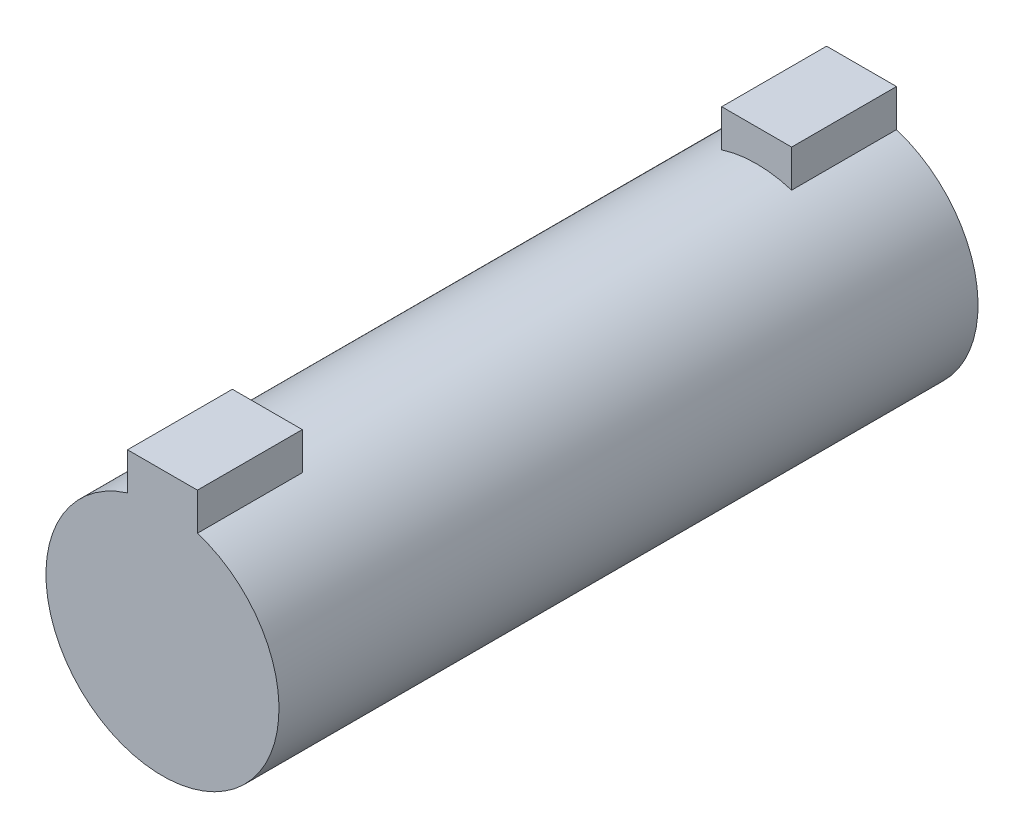
SolidWorks part; units mm, degrees
material "AISI 1010 Steel, hot rolled bar"
ref_plane "Front Plane" through (0, 0, 0) normal (0, 0, 1) x (1, 0, 0)
ref_plane "Top Plane" through (0, 0, 0) normal (0, 1, 0) x (1, 0, 0)
ref_plane "Right Plane" through (0, 0, 0) normal (1, 0, 0) x (0, 0, -1)
sketch "Sketch1" plane through (0, 0, 0) normal (0, 0, 1) x (1, 0, 0)
  circle A0 centre (0, 0) radius 10
  dimension "D1" = 20
extrude "Boss-Extrude1" add sketch "Sketch1" along normal mid plane 60
sketch "Sketch2" plane through (0, 0, 30) normal (0, 0, 1) x (1, 0, 0)
  line L2 (3, 12.745) -> (-3, 12.745)
  line L3 (3, 12.745) -> (3, 9.485)
  line L4 (3, 9.485) -> (-3, 9.485)
  line L5 (-3, 12.745) -> (-3, 9.485)
  line L6 (3, 12.745) -> (-3, 9.485) construction
  line L7 (3, 9.485) -> (-3, 12.745) construction
  point P0 (0, 11.115)
  point P1 (-0.0734, 11.1162)
  point P3 (0, 0)
  point P4 (0, 0)
  point P10 (0, 0)
  point P11 (0, 0)
  point P12 (0, 0)
  point P13 (0, 0)
  point P14 (2.9344, 9.5185)
  point P15 (0, 0)
  point P17 (0, 0)
  point P19 (3, 9.485)
  point P20 (0, 9.485)
  point P21 (3, 9.5394)
  dimension "D1" = 3.26
  dimension "D2" = 6
extrude "Boss-Extrude2" add sketch "Sketch2" against normal blind 9
mirror "Mirror1" about plane through (0, 0, 0) normal (0, 0, 1) of "Boss-Extrude2"
